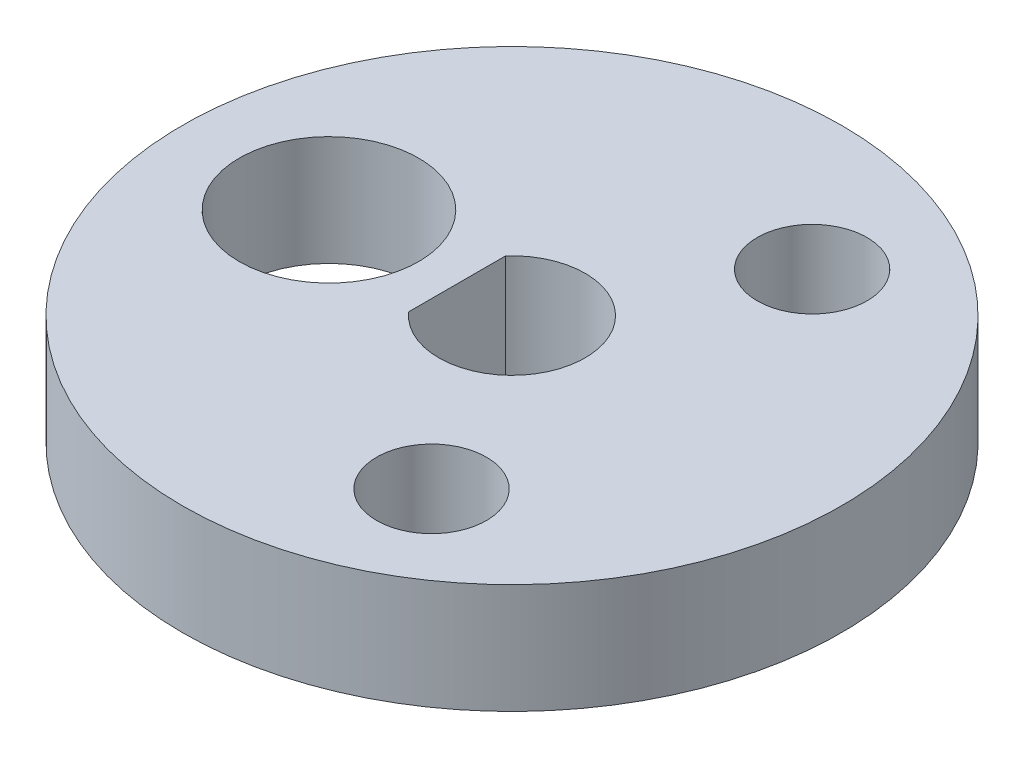
SolidWorks part; units mm, degrees
ref_plane "Front Plane" through (0, 0, 0) normal (0, 0, 1) x (1, 0, 0)
ref_plane "Top Plane" through (0, 0, 0) normal (0, 1, 0) x (1, 0, 0)
ref_plane "Right Plane" through (0, 0, 0) normal (1, 0, 0) x (0, 0, -1)
sketch "Sketch1" plane through (0, 0, 0) normal (0, 1, 0) x (1, 0, 0)
  line L0 (-1.4998, 1.3231) -> (-1.5002, -1.3226)
  arc A0 (-1.5002, -1.3226) -> (-1.4998, 1.3231) centre (0, 0) ccw
  circle A1 centre (-5, 0.0008) radius 2.45
  circle A2 centre (0, 0) radius 9
  circle A3 centre (2.9991, -5.1967) radius 1.5
  circle A4 centre (3.0009, 5.1957) radius 1.5
  dimension "D1" = 18
  dimension "D3" = 4.9
  dimension "D2" = 5
extrude "Boss-Extrude1" add sketch "Sketch1" along normal blind 3
